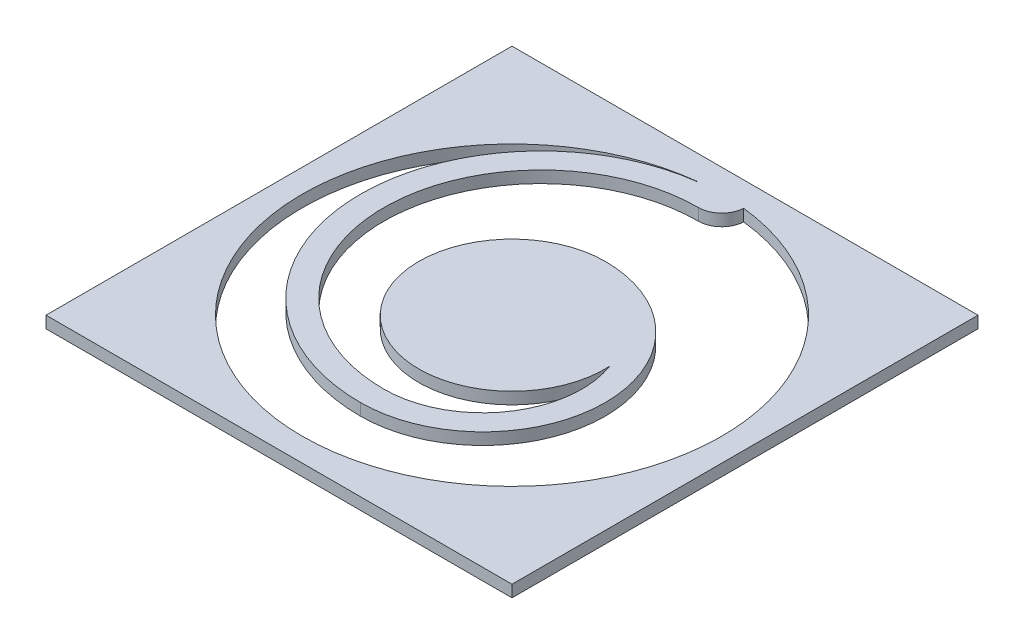
SolidWorks part; units mm, degrees
ref_plane "Front Plane" through (0, 0, 0) normal (0, 0, 1) x (1, 0, 0)
ref_plane "Top Plane" through (0, 0, 0) normal (0, 1, 0) x (1, 0, 0)
ref_plane "Right Plane" through (0, 0, 0) normal (1, 0, 0) x (0, 0, -1)
sketch "Sketch1" plane through (0, 0, 0) normal (0, 1, 0) x (1, 0, 0)
  line L0 (2.5, 1.5) -> (2.5, 0.25) construction
  line L1 (0, 0) -> (5, 0)
  line L2 (0, 0) -> (0, 5)
  line L3 (0, 5) -> (5, 5)
  line L4 (5, 0) -> (5, 5)
  line L5 (2.5, 0.875) -> (2.5, 4.75) construction
  line L6 (2.5, 3.5) -> (2.5, 0.875)
  circle A0 centre (2.5, 2.5) radius 1
  circle A1 centre (2.5, 2.5) radius 2.25
  arc A4 (2.2505, 4.7339) -> (2.5, 0.875) centre (2.5, 2.8125) ccw
  arc A5 (2.5, 0.875) -> (2.5, 3.5) centre (2.5, 2.1875) ccw
  arc A6 (2.5, 4.5) -> (2.5, 1.125) centre (2.5, 2.8125) ccw
  arc A7 (1.5013, 2.55) -> (3.4987, 2.55) centre (2.5, 2.1875) ccw
  arc A8 (2.2504, 4.7361) -> (2.2505, 4.7339) centre (2.5, 4.75) ccw
  arc A9 (2.5, 4.5) -> (2.7496, 4.7361) centre (2.5, 4.75) ccw
  point P8 (2.5, 5)
  point P9 (5, 2.5)
  point P36 (2.5, 2.5)
  dimension "D3" = 2
  dimension "D4" = 4.5
  dimension "D5" = 0.25
  dimension "D6" = 0.25
  dimension "D1" = 5
  dimension "D2" = 5
extrude "Boss-Extrude1" add sketch "Sketch1" along normal blind 0.127 contours L1 L4 L3 L2 A1 | A6 A9 A1 A4 L6 | A7 L6 A5 A0 | L6 A0 | L6 A0
